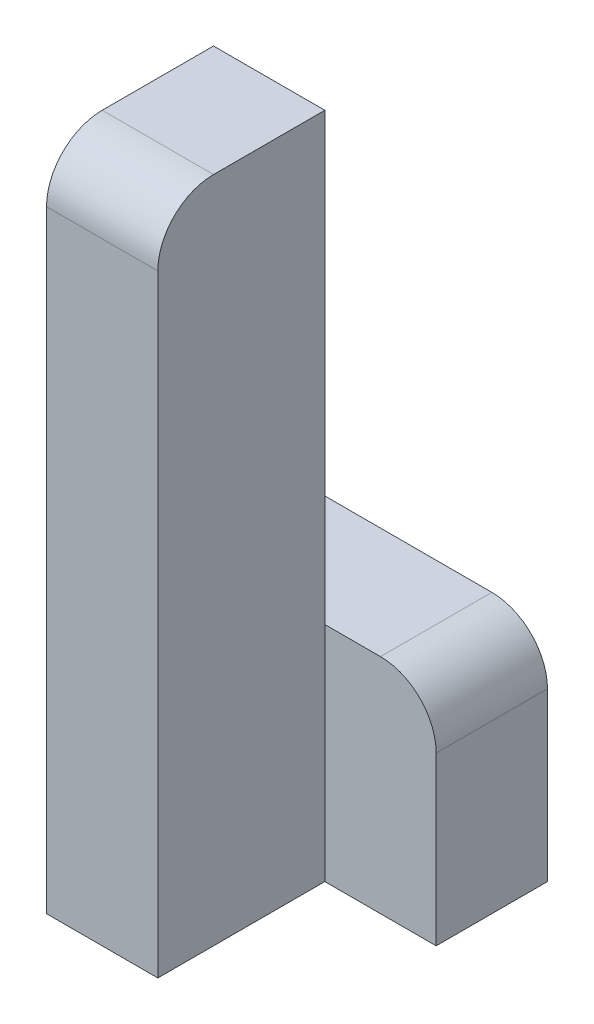
SolidWorks part; units mm, degrees
ref_plane "Front Plane" through (0, 0, 0) normal (0, 0, 1) x (1, 0, 0)
ref_plane "Top Plane" through (0, 0, 0) normal (0, 1, 0) x (1, 0, 0)
ref_plane "Right Plane" through (0, 0, 0) normal (1, 0, 0) x (0, 0, -1)
sketch "Sketch1" plane through (0, 0, 0) normal (0, 0, 1) x (1, 0, 0)
  line L1 (-30, -120) -> (-10, -120)
  line L2 (-10, -120) -> (-10, 0)
  line L3 (-10, 0) -> (-30, 0)
  line L4 (-30, 0) -> (-30, -120)
  dimension "D1" = 20
  dimension "Width" = 120
extrude "Boss-Extrude1" add sketch "Sketch1" along normal blind 30
sketch "Sketch2" plane through (0, 0, 0) normal (0, 0, 1) x (1, 0, 0)
  line L1 (-30, -120) -> (10, -120)
  line L2 (10, -120) -> (10, -80)
  line L3 (10, -80) -> (-30, -80)
  line L4 (-30, -80) -> (-30, -120)
  dimension "D1" = 40
  dimension "Width" = 40
extrude "Boss-Extrude2" add sketch "Sketch2" against normal blind 20
fillet "Fillet1" radius 10 2 edges at (10, -80, -10) (-20, 0, 30)
